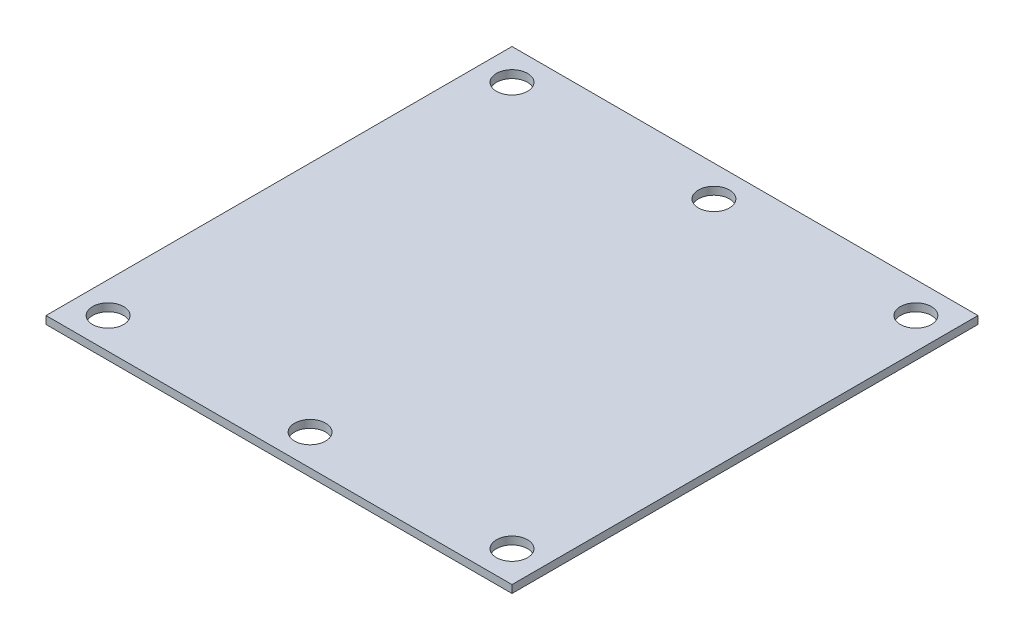
SolidWorks part; units mm, degrees
ref_plane "Front Plane" through (0, 0, 0) normal (0, 0, 1) x (1, 0, 0)
ref_plane "Top Plane" through (0, 0, 0) normal (0, 1, 0) x (1, 0, 0)
ref_plane "Right Plane" through (0, 0, 0) normal (1, 0, 0) x (0, 0, -1)
sketch "Sketch1" plane through (0, 0, 0) normal (0, 1, 0) x (1, 0, 0)
  line L1 (30, -30) -> (-30, -30)
  line L2 (30, -30) -> (30, 30)
  line L3 (30, 30) -> (-30, 30)
  line L4 (-30, -30) -> (-30, 30)
  line L5 (30, -30) -> (-30, 30) construction
  line L6 (30, 30) -> (-30, -30) construction
  point P0 (0, 0)
  dimension "D1" = 60
  dimension "D2" = 60
extrude "Boss-Extrude1" add sketch "Sketch1" along normal blind 1
hole_wizard "Ø4.0 (4) Diameter Hole1" positions "Sketch13" profile "Sketch12" hole size "Ø4.0" standard "ANSI Metric" end condition up to next
sketch "Sketch13" plane through (0, 1, 0) normal (0, 1, 0) x (1, 0, 0)
  line L0 (0, 30) -> (0, -30) construction
  line L1 (30, 30) -> (-30, 30) construction
  line L2 (-30, -30) -> (30, -30) construction
  line L4 (-30, 0) -> (30, 0) construction
  line L5 (-30, 30) -> (-30, -30) construction
  line L6 (30, -30) -> (30, 30) construction
  point P17 (26, 26)
  point P24 (0, 26)
  point P27 (-26, 26)
  point P28 (0, -26)
  point P29 (26, -26)
  point P30 (-26, -26)
  dimension "D1" = 4
  dimension "D2" = 4
sketch "Sketch12" plane through (26, 1, -26) normal (1, 0, 0) x (0, 0, 1)
  line L0 (0, 0) -> (0, 1)
  line L1 (0, 1) -> (2, 1)
  line L2 (2, 1) -> (2, 0)
  line L5 (2, 0) -> (0, 0)
  line L11 (0, -6.35) -> (0, 107.95) construction
  dimension "Thru Hole Dia." = 4
  dimension "Thru Hole Depth" = 1
